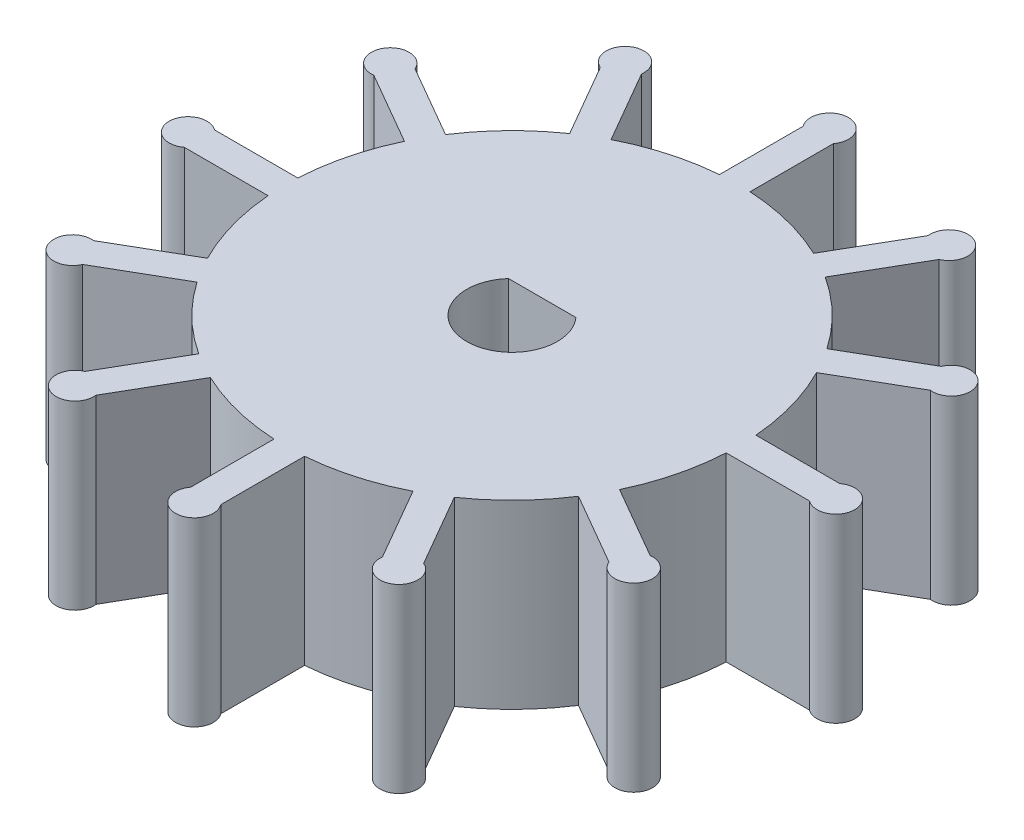
SolidWorks part; units mm, degrees
ref_plane "Front Plane" through (0, 0, 0) normal (0, 0, 1) x (1, 0, 0)
ref_plane "Top Plane" through (0, 0, 0) normal (0, 1, 0) x (1, 0, 0)
ref_plane "Right Plane" through (0, 0, 0) normal (1, 0, 0) x (0, 0, -1)
sketch "Sketch1" plane through (0, 0, 0) normal (0, 1, 0) x (1, 0, 0)
  line L9 (-1.2099, 20.499) -> (-1.2099, 14.9511)
  line L10 (0.7901, 20.499) -> (0.7901, 14.9792)
  line L11 (9.2016, 18.3576) -> (6.4277, 13.553)
  line L12 (10.9337, 17.3576) -> (8.1738, 12.5773)
  line L13 (17.1477, 11.2973) -> (12.3431, 8.5234)
  line L14 (18.1477, 9.5653) -> (13.3674, 6.8054)
  line L15 (20.499, 1.2099) -> (14.9511, 1.2099)
  line L16 (20.499, -0.7901) -> (14.9792, -0.7901)
  line L17 (18.3576, -9.2016) -> (13.553, -6.4277)
  line L18 (17.3576, -10.9337) -> (12.5773, -8.1738)
  line L19 (11.2973, -17.1477) -> (8.5234, -12.3431)
  line L20 (9.5653, -18.1477) -> (6.8054, -13.3674)
  line L21 (1.2099, -20.499) -> (1.2099, -14.9511)
  line L22 (-0.7901, -20.499) -> (-0.7901, -14.9792)
  line L23 (-9.2016, -18.3576) -> (-6.4277, -13.553)
  line L24 (-10.9337, -17.3576) -> (-8.1738, -12.5773)
  line L25 (-17.1477, -11.2973) -> (-12.3431, -8.5234)
  line L26 (-18.1477, -9.5653) -> (-13.3674, -6.8054)
  line L27 (-20.499, -1.2099) -> (-14.9511, -1.2099)
  line L28 (-20.499, 0.7901) -> (-14.9792, 0.7901)
  line L29 (-18.3576, 9.2016) -> (-13.553, 6.4277)
  line L30 (-17.3576, 10.9337) -> (-12.5773, 8.1738)
  line L31 (-11.2973, 17.1477) -> (-8.5234, 12.3431)
  line L32 (-9.5653, 18.1477) -> (-6.8054, 13.3674)
  arc A8 (6.4277, 13.553) -> (0.7901, 14.9792) centre (0, 0) ccw
  arc A9 (0.7901, 20.499) -> (-1.2099, 20.499) centre (-0.2099, 21.249) ccw
  arc A10 (10.9337, 17.3576) -> (9.2016, 18.3576) centre (10.4427, 18.5071) ccw
  arc A11 (18.1477, 9.5653) -> (17.1477, 11.2973) centre (18.2972, 10.8063) ccw
  arc A12 (20.499, -0.7901) -> (20.499, 1.2099) centre (21.249, 0.2099) ccw
  arc A13 (17.3576, -10.9337) -> (18.3576, -9.2016) centre (18.5071, -10.4427) ccw
  arc A14 (9.5653, -18.1477) -> (11.2973, -17.1477) centre (10.8063, -18.2972) ccw
  arc A15 (-0.7901, -20.499) -> (1.2099, -20.499) centre (0.2099, -21.249) ccw
  arc A16 (-10.9337, -17.3576) -> (-9.2016, -18.3576) centre (-10.4427, -18.5071) ccw
  arc A17 (-18.1477, -9.5653) -> (-17.1477, -11.2973) centre (-18.2972, -10.8063) ccw
  arc A18 (-20.499, 0.7901) -> (-20.499, -1.2099) centre (-21.249, -0.2099) ccw
  arc A19 (-17.3576, 10.9337) -> (-18.3576, 9.2016) centre (-18.5071, 10.4427) ccw
  arc A20 (-9.5653, 18.1477) -> (-11.2973, 17.1477) centre (-10.8063, 18.2972) ccw
  arc A21 (12.3431, 8.5234) -> (8.1738, 12.5773) centre (0, 0) ccw
  arc A22 (14.9511, 1.2099) -> (13.3674, 6.8054) centre (0, 0) ccw
  arc A23 (-8.5234, 12.3431) -> (-12.5773, 8.1738) centre (0, 0) ccw
  arc A24 (-13.553, 6.4277) -> (-14.9792, 0.7901) centre (0, 0) ccw
  arc A25 (-14.9511, -1.2099) -> (-13.3674, -6.8054) centre (0, 0) ccw
  arc A26 (-12.3431, -8.5234) -> (-8.1738, -12.5773) centre (0, 0) ccw
  arc A27 (-6.4277, -13.553) -> (-0.7901, -14.9792) centre (0, 0) ccw
  arc A28 (1.2099, -14.9511) -> (6.8054, -13.3674) centre (0, 0) ccw
  arc A29 (8.5234, -12.3431) -> (12.5773, -8.1738) centre (0, 0) ccw
  arc A30 (13.553, -6.4277) -> (14.9792, -0.7901) centre (0, 0) ccw
  arc A31 (-1.2099, 14.9511) -> (-6.8054, 13.3674) centre (0, 0) ccw
  point P1 (-14.8816, 1.8806)
  point P53 (0, 0)
  point P68 (0, 0)
  dimension "D1" = 1.25
  dimension "D2" = 12
  dimension "D3" = 2
  dimension "D4" = 8
  dimension "D5" = 21.25
  dimension "D6" = 5.5478
  dimension "D7" = 1
  dimension "D8" = 1
extrude "Boss-Extrude1" add sketch "Sketch1" along normal blind 12
sketch "Sketch2" plane through (0, 12, 0) normal (0, 1, 0) x (1, 0, 0)
  line L0 (-2.2361, 2) -> (2.2361, 2)
  arc A0 (-2.2361, 2) -> (2.2361, 2) centre (0, 0) ccw
  dimension "D1" = 3
  dimension "D2" = 2
extrude "Cut-Extrude1" cut sketch "Sketch2" against normal through all
